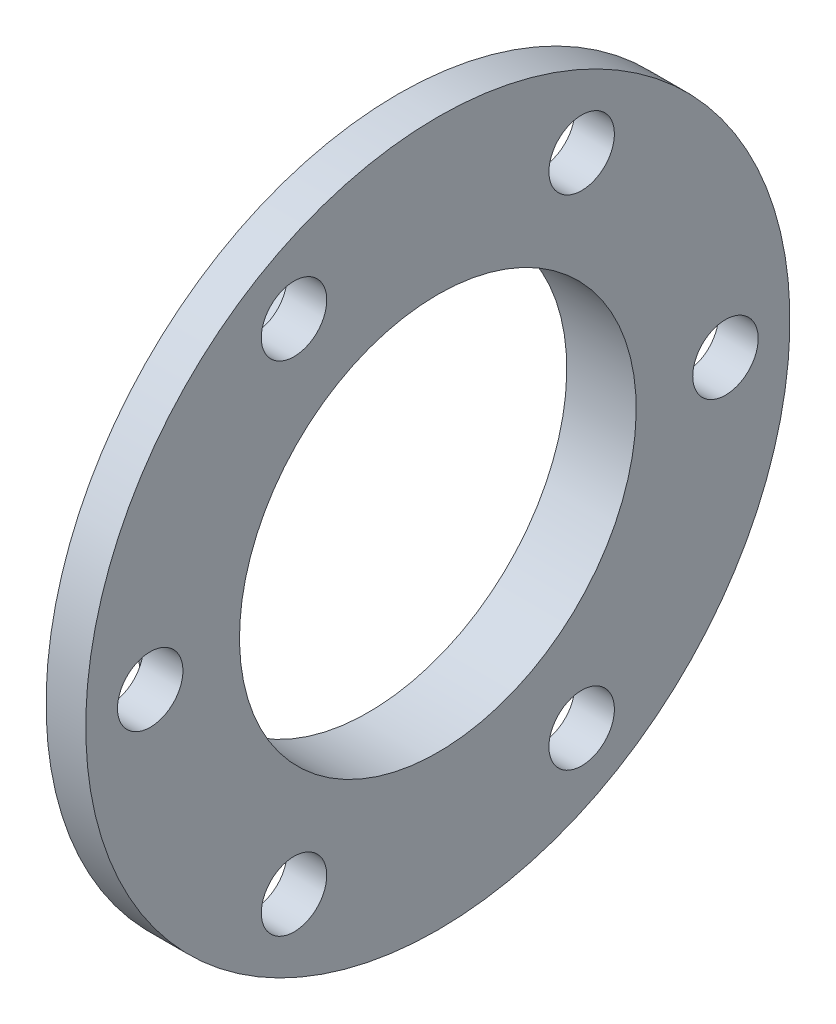
SolidWorks part; units mm, degrees
material "1.0036 (S235JRG1)"
ref_plane "Front Plane" through (0, 0, 0) normal (0, 0, 1) x (1, 0, 0)
ref_plane "Top Plane" through (0, 0, 0) normal (0, 1, 0) x (1, 0, 0)
ref_plane "Right Plane" through (0, 0, 0) normal (1, 0, 0) x (0, 0, -1)
sketch "Sketch2" plane through (0, 0, 0) normal (0, 0, 1) x (1, 0, 0)
  line L0 (0, 0) -> (-7, 0) construction
  line L1 (-7, 0) -> (-7, 23.5)
  line L2 (-7, 23.5) -> (-4, 23.5)
  line L3 (-4, 23.5) -> (-4, 35.5)
  line L4 (-4, 35.5) -> (0, 35.5)
  line L5 (0, 35.5) -> (0, 0)
  line L6 (0, 0) -> (-7, 0) construction
  line L8 (-7, 20) -> (0, 20)
  dimension "D1" = 4
  dimension "D2" = 3
  dimension "D3" = 47
  dimension "D4" = 12
  dimension "D5" = 40
revolve "Revolve1" add sketch "Sketch2" angle 360 about L0
sketch "Sketch3" plane through (-4, 0, 0) normal (-1, 0, 0) x (0, 0, 1)
  point P0 (-29, 0)
  dimension "D1" = 29
hole_wizard "M6 Clearance Hole1" positions "3DSketch1" profile "Sketch4" hole size "M6" standard "ISO" end condition up to next
sketch3d "3DSketch1"
  point P0 (-4, 0, -29)
sketch "Sketch4" plane through (-4, 0, -29) normal (0, 1, 0) x (0, 0, 1)
  line L0 (0, 0) -> (0, 4)
  line L1 (0, 4) -> (3.3, 4)
  line L2 (3.3, 4) -> (3.3, 0)
  line L5 (3.3, 0) -> (0, 0)
  line L11 (0, -6.35) -> (0, 107.95) construction
  dimension "Thru Hole Dia." = 6.6
  dimension "Thru Hole Depth" = 4
pattern_circular "CirPattern1" count 6 over 360 about axis through (0, 0, 0) along (1, 0, 0) of "M6 Clearance Hole1"
